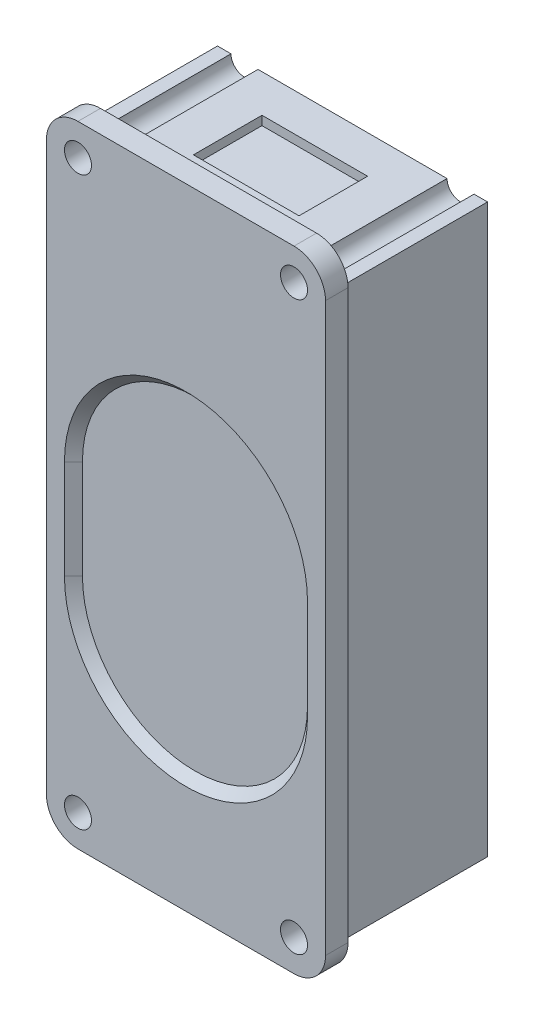
SolidWorks part; units mm, degrees
ref_plane "Front Plane" through (0, 0, 0) normal (0, 0, 1) x (1, 0, 0)
ref_plane "Top Plane" through (0, 0, 0) normal (0, 1, 0) x (1, 0, 0)
ref_plane "Right Plane" through (0, 0, 0) normal (1, 0, 0) x (0, 0, -1)
sketch "Sketch1" plane through (0, 0, 0) normal (0, 0, 1) x (1, 0, 0)
  line L1 (-12, 35) -> (12, 35)
  line L2 (-15.5, 31.5) -> (-15.5, -31.5)
  line L3 (-12, -35) -> (12, -35)
  line L4 (15.5, 31.5) -> (15.5, -31.5)
  line L5 (-15.5, 35) -> (15.5, -35) construction
  line L6 (-15.5, -35) -> (15.5, 35) construction
  arc A0 (12, -35) -> (15.5, -31.5) centre (12, -31.5) ccw
  arc A1 (-15.5, -31.5) -> (-12, -35) centre (-12, -31.5) ccw
  arc A2 (-12, 35) -> (-15.5, 31.5) centre (-12, 31.5) ccw
  arc A3 (12, 35) -> (15.5, 31.5) centre (12, 31.5) cw
  point P0 (0, 0)
  dimension "D3" = 3.5
  dimension "D1" = 31
  dimension "D2" = 70
extrude "Boss-Extrude1" add sketch "Sketch1" along normal blind 2.5
sketch "Sketch3" plane through (0, 0, 0) normal (1, 0, 0) x (0, 0, -1)
  line L0 (0, -35) -> (0, -31.5) construction
  line L1 (0, -31.5) -> (16, -31.5)
  line L2 (0, -31.5) -> (0, 31.5)
  line L3 (0, 31.5) -> (16, 31.5)
  line L4 (16, -31.5) -> (16, 31.5)
  line L5 (0, -31.5) -> (16, 31.5) construction
  line L6 (0, 31.5) -> (16, -31.5) construction
  point P0 (8, 0)
  dimension "D1" = 16
  dimension "D2" = 63
extrude "Boss-Extrude2" add sketch "Sketch3" along normal mid plane 30
sketch "Sketch2" plane through (0, 0, 0) normal (0, 0, 1) x (1, 0, 0)
  line L0 (0, 0) -> (0, -29.7647) construction
  line L2 (-12, -35) -> (12, -35) construction
  line L3 (0, 0) -> (12.7, 0) construction
  circle A0 centre (-12, -31.5) radius 1.5
  circle A1 centre (12, -31.5) radius 1.5
  circle A2 centre (12, 31.5) radius 1.5
  circle A3 centre (-12, 31.5) radius 1.5
  dimension "D1" = 24
  dimension "D2" = 3.5
  dimension "D3" = 3
extrude "Cut-Extrude1" cut sketch "Sketch2" against normal through all both and the other way through all
ref_plane "Plane1" through (0, 0, 2.5) normal (0, 0, -1) x (-1, 0, 0)
sketch "Sketch4" plane through (0, 0, 2.5) normal (0, 0, 1) x (1, 0, 0)
  line L0 (0, 1.5) -> (0, -9.5) construction
  line L1 (13.5, 1.5) -> (13.5, -9.5)
  line L2 (-13.5, 1.5) -> (-13.5, -9.5)
  line L3 (-12, -35) -> (12, -35) construction
  arc A0 (13.5, 1.5) -> (-13.5, 1.5) centre (0, 1.5) ccw
  arc A1 (-13.5, -9.5) -> (13.5, -9.5) centre (0, -9.5) ccw
  point P2 (0, -4)
  point P8 (0, -23)
  point P9 (0, 15)
  dimension "D1" = 38
  dimension "D2" = 27
  dimension "D3" = 12
extrude "Cut-Extrude2" cut sketch "Sketch4" against normal blind 1 draft 45
sketch "Sketch5" plane through (0, 31.5, 0) normal (0, 1, 0) x (1, 0, 0)
  line L0 (0, 0) -> (0, 16) construction
  line L1 (10.5, 16) -> (-10.5, 16) construction
  line L3 (-5.8663, 11.808) -> (5.8663, 11.808)
  line L4 (-5.8663, 11.808) -> (-5.8663, 4.192)
  line L5 (-5.8663, 4.192) -> (5.8663, 4.192)
  line L6 (5.8663, 11.808) -> (5.8663, 4.192)
  line L7 (-5.8663, 11.808) -> (5.8663, 4.192) construction
  line L8 (-5.8663, 4.192) -> (5.8663, 11.808) construction
  point P5 (0, 8)
extrude "Cut-Extrude3" cut sketch "Sketch5" against normal blind 1
